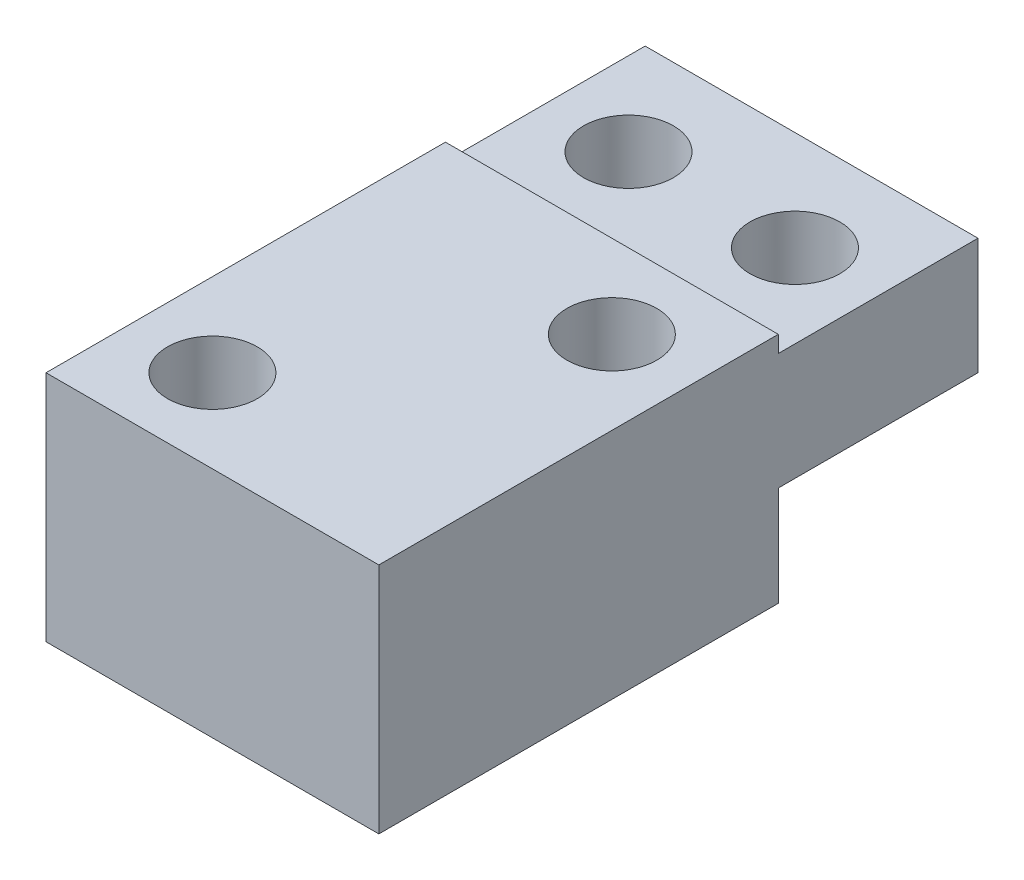
SolidWorks part; units mm, degrees
material "AISI 316 Stainless Steel Sheet (SS)"
ref_plane "Front Plane" through (0, 0, 0) normal (0, 0, 1) x (1, 0, 0)
ref_plane "Top Plane" through (0, 0, 0) normal (0, 1, 0) x (1, 0, 0)
ref_plane "Right Plane" through (0, 0, 0) normal (1, 0, 0) x (0, 0, -1)
sketch "Sketch1" plane through (0, 0, 0) normal (0, 1, 0) x (1, 0, 0)
  line L1 (-5, 9) -> (5, 9)
  line L2 (-5, 9) -> (-5, -9)
  line L3 (-5, -9) -> (5, -9)
  line L4 (5, 9) -> (5, -9)
  point P4 (0, -9)
  point P6 (-5, 0)
  dimension "D1" = 10
  dimension "D2" = 18
extrude "Boss-Extrude1" add sketch "Sketch1" along normal blind 7
sketch "Sketch2" plane through (0, 7, 0) normal (0, 1, 0) x (1, 0, 0)
  line L0 (5, -9) -> (5, 9) construction
  line L1 (-5, 9) -> (5, 9)
  line L2 (-5, 9) -> (-5, 3)
  line L3 (-5, 3) -> (5, 3)
  line L4 (5, 9) -> (5, 3)
  dimension "D1" = 6
extrude "Cut-Extrude1" cut sketch "Sketch2" against normal blind 0.5
hole_wizard "M2.5 Clearance Hole1" positions "Sketch3" profile "Sketch4" hole size "M2.5" standard "ISO" end condition through all
sketch "Sketch3" plane through (0, 7, 0) normal (0, 1, 0) x (1, 0, 0)
  line L0 (-5, -9) -> (5, -9) construction
  line L1 (-5, 3) -> (-5, -9) construction
  line L2 (5, -9) -> (5, 3) construction
  line L4 (-5, 3) -> (5, 3) construction
  point P0 (-2.5, -6.5)
  point P2 (2.5, 0.5)
  dimension "D1" = 2.5
  dimension "D2" = 2.5
  dimension "D3" = 2.5
  dimension "D4" = 2.5
sketch "Sketch4" plane through (-2.5, 7, 6.5) normal (1, 0, 0) x (0, 0, 1)
  line L0 (0, 0) -> (0, 7)
  line L1 (0, 7) -> (1.35, 7)
  line L2 (1.35, 7) -> (1.35, 0)
  line L5 (1.35, 0) -> (0, 0)
  line L11 (0, -6.35) -> (0, 107.95) construction
  dimension "Thru Hole Dia." = 2.7
  dimension "Thru Hole Depth" = 7
sketch "Sketch5" plane through (0, 0, 0) normal (0, -1, 0) x (1, 0, 0)
  line L0 (-5, -9) -> (-5, 9) construction
  line L1 (5, -9) -> (-5, -9)
  line L2 (5, -9) -> (5, -3)
  line L3 (5, -3) -> (-5, -3)
  line L4 (-5, -9) -> (-5, -3)
  line L5 (-5, -3) -> (5, -3) construction
  line L6 (-5, -3) -> (5, -3)
  line M5 (-5, 9) -> (-5, -9)
  line M6 (-5, -9) -> (5, -9)
  line M7 (5, -9) -> (5, 9)
extrude "Cut-Extrude2" cut sketch "Sketch5" against normal blind 3 contours L3 M7 M5 M6
hole_wizard "M2.5 Clearance Hole2" positions "Sketch6" profile "Sketch7" hole size "M2.5" standard "ISO" end condition through all
sketch "Sketch6" plane through (0, 3, 0) normal (0, -1, 0) x (-1, 0, 0)
  line L0 (-5, 9) -> (-5, 3) construction
  line L1 (-5, 9) -> (-5, 3)
  line L2 (5, 3) -> (5, 9) construction
  point P0 (-2.5, 6)
  point P2 (2.5, 6)
  point P7 (-5, 6)
  point P11 (5, 6)
  dimension "D1" = 2.5
  dimension "D2" = 2.5
sketch "Sketch7" plane through (2.5, 3, -6) normal (1, 0, 0) x (0, 0, -1)
  line L0 (0, 0) -> (0, 4)
  line L1 (0, 4) -> (1.35, 4)
  line L2 (1.35, 4) -> (1.35, 0)
  line L5 (1.35, 0) -> (0, 0)
  line L11 (0, -6.35) -> (0, 107.95) construction
  dimension "Thru Hole Dia." = 2.7
  dimension "Thru Hole Depth" = 4
